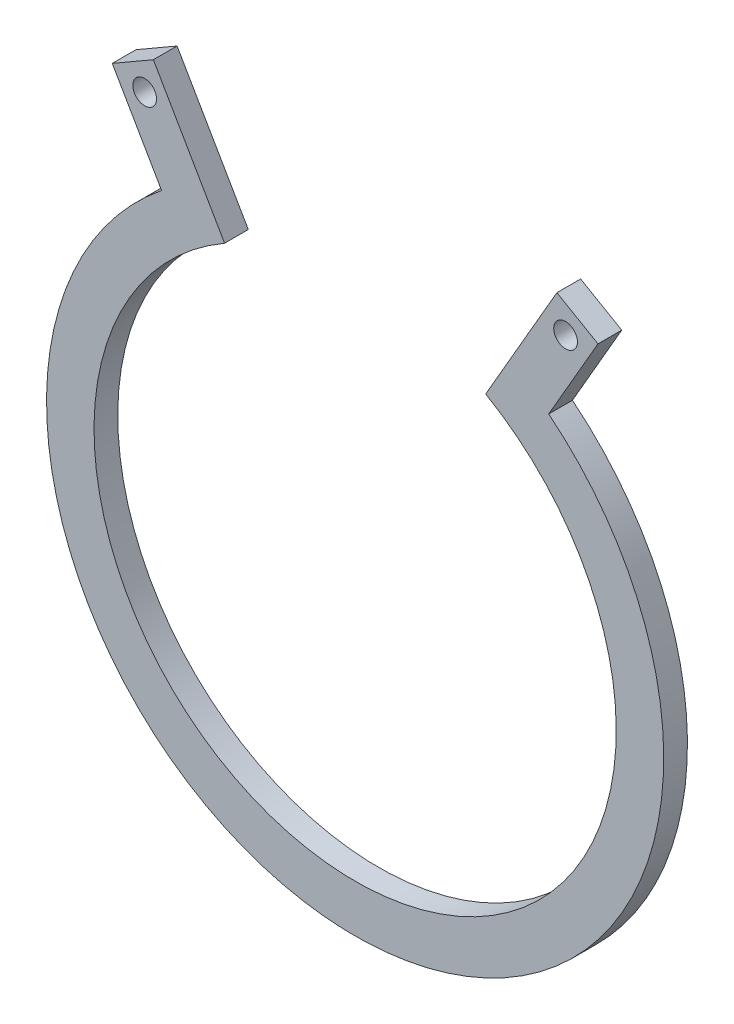
SolidWorks part; units mm, degrees
ref_plane "Front Plane" through (0, 0, 0) normal (0, 0, 1) x (1, 0, 0)
ref_plane "Top Plane" through (0, 0, 0) normal (0, 1, 0) x (1, 0, 0)
ref_plane "Right Plane" through (0, 0, 0) normal (1, 0, 0) x (0, 0, -1)
sketch "Sketch2" plane through (0, 0, 0) normal (0, 0, 1) x (1, 0, 0)
  circle A0 centre (0, 0) radius 38.1
  circle A1 centre (0, 0) radius 41.275
  circle A2 centre (0, 0) radius 34.925
  dimension "D1" = 76.2
  dimension "D2" = 3.175
  dimension "D3" = 3.175
extrude "Boss-Extrude1" add sketch "Sketch2" along normal blind 3.175 contours A1 A0 | A0 A2
sketch "Sketch3" plane through (0, 0, 3.175) normal (0, 0, 1) x (1, 0, 0)
  line L0 (-29.7371, 45.1562) -> (-28.1496, 42.4066) construction
  line L1 (0, 0) -> (-20.6375, 35.7452) construction
  line L2 (0, 0) -> (0, 41.275) construction
  line L3 (-20.6375, 35.7452) -> (-26.9875, 46.7437)
  line L4 (-26.9875, 46.7437) -> (-32.4868, 43.5687)
  line L5 (-32.4868, 43.5687) -> (-25.8911, 32.1446)
  line L6 (-26.9875, 46.7437) -> (-20.3918, 35.3196)
  line L7 (-26.1368, 32.5702) -> (-32.4868, 43.5687)
  line L8 (29.7371, 45.1562) -> (28.1496, 42.4066) construction
  line L9 (26.1368, 32.5702) -> (32.4868, 43.5687)
  line L10 (26.9875, 46.7437) -> (20.3918, 35.3196)
  line L11 (32.4868, 43.5687) -> (25.8911, 32.1446)
  line L12 (26.9875, 46.7437) -> (32.4868, 43.5687)
  line L13 (20.6375, 35.7452) -> (26.9875, 46.7437)
  circle A0 centre (0, 0) radius 41.275 construction
  circle A2 centre (-28.1496, 42.4066) radius 1.5875
  circle A3 centre (28.1496, 42.4066) radius 1.5875
  circle M7 centre (0, 0) radius 41.275
  dimension "D5" = 3.175
  dimension "D1" = 30
  dimension "D2" = 3.175
  dimension "D3" = 12.7
  dimension "D4" = 6.35
extrude "Boss-Extrude2" add sketch "Sketch3" against normal up to surface (3.175 mm away) contours L4 L5 L3 A2 M7 | L12 L10 L11 L9 A3 M7 up to face at (41.275, 0, 0)
ref_plane "Plane4" through (-26.9875, 46.7437, 3.175) normal (0, 0, 1) x (1, 0, 0)
sketch "Sketch5" plane through (0, 0, 3.175) normal (0, 0, 1) x (1, 0, 0)
  line L0 (-20.6375, 35.7452) -> (0, 0)
  line L1 (0, 0) -> (20.6375, 35.7452)
  arc A0 (20.6375, 35.7452) -> (-20.6375, 35.7452) centre (0, 0) ccw construction
  arc A1 (20.6375, 35.7452) -> (-20.6375, 35.7452) centre (0, 0) ccw
extrude "Cut-Extrude1" cut sketch "Sketch5" against normal up to surface (3.175 mm away) up to face at (0, 31.0643, 0)
